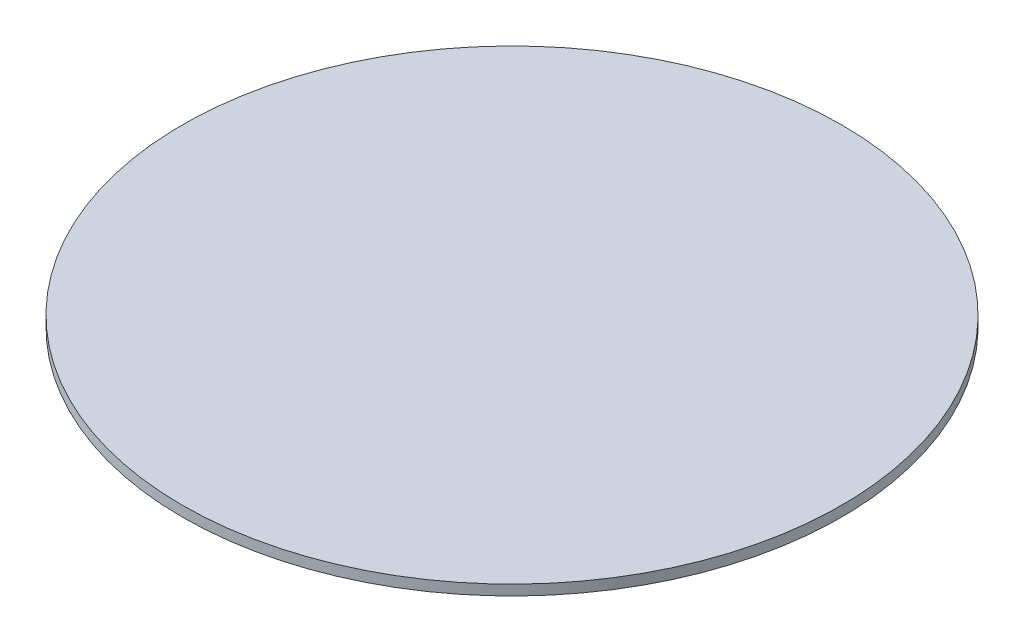
SolidWorks part; units mm, degrees
ref_plane "Front Plane" through (0, 0, 0) normal (0, 0, 1) x (1, 0, 0)
ref_plane "Top Plane" through (0, 0, 0) normal (0, 1, 0) x (1, 0, 0)
ref_plane "Right Plane" through (0, 0, 0) normal (1, 0, 0) x (0, 0, -1)
sketch "Sketch1" plane through (0, 0, 0) normal (0, 1, 0) x (1, 0, 0)
  circle A0 centre (0, 0) radius 16
  dimension "D1" = 32
extrude "Boss-Extrude1" add sketch "Sketch1" along normal blind 0.5
